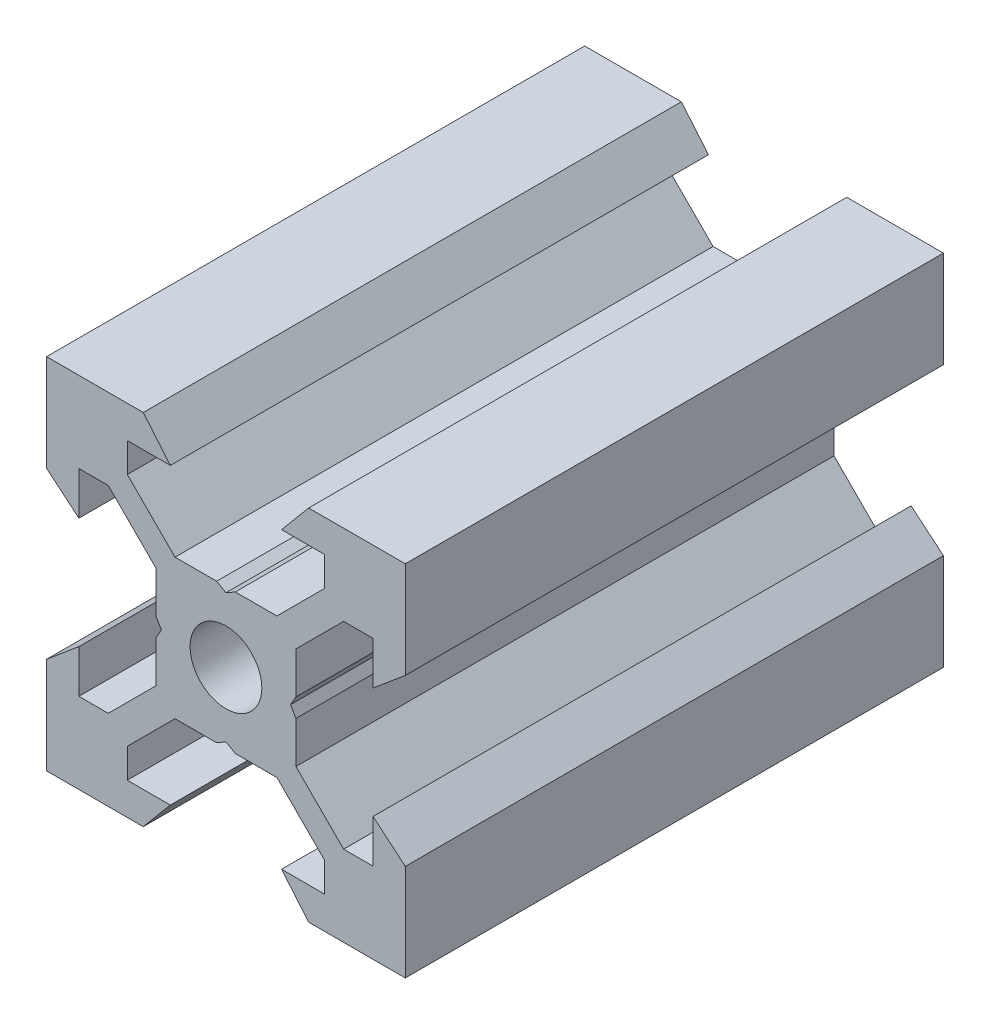
SolidWorks part; units mm, degrees
ref_plane "Front Plane" through (0, 0, 0) normal (0, 0, 1) x (1, 0, 0)
ref_plane "Top Plane" through (0, 0, 0) normal (0, 1, 0) x (1, 0, 0)
ref_plane "Right Plane" through (0, 0, 0) normal (1, 0, 0) x (0, 0, -1)
sketch "Sketch1" plane through (0, 0, 0) normal (0, 0, 1) x (1, 0, 0)
  line L0 (10, 10) -> (4.6104, 10) construction
  line L1 (10, 10) -> (10, 4.6104) construction
  line L2 (10, -10) -> (10, -4.6104) construction
  line L3 (10, -10) -> (4.6104, -10) construction
  line L4 (10, 10) -> (10, 4.6104)
  line L5 (6.5607, 5.5) -> (8.2, 5.5)
  line L6 (5.5, 8.2) -> (5.5, 6.5607)
  line L7 (10, 10) -> (4.6104, 10)
  line L8 (10, 10) -> (10, 4.6104)
  line L9 (6.5607, 5.5) -> (3.9, 2.8393)
  line L10 (5.5, 6.5607) -> (2.8393, 3.9)
  line L11 (10, 4.6104) -> (8.2, 3.1)
  line L12 (4.6104, 10) -> (3.1, 8.2)
  line L13 (8.2, 3.1) -> (8.2, 5.5)
  line L14 (3.1, 8.2) -> (5.5, 8.2)
  line L15 (-6.5607, 5.5) -> (-8.2, 5.5)
  line L16 (6.5607, -5.5) -> (8.2, -5.5)
  line L17 (3.1, -8.2) -> (5.5, -8.2)
  line L18 (8.2, -3.1) -> (8.2, -5.5)
  line L19 (4.6104, -10) -> (3.1, -8.2)
  line L20 (10, -4.6104) -> (8.2, -3.1)
  line L21 (0.5196, -3.9) -> (0, -3.6)
  line L22 (0.5196, 3.9) -> (0, 3.6)
  line L23 (3.6, 0) -> (3.9, -0.5196)
  line L24 (3.9, 0.5196) -> (3.6, 0)
  line L25 (3.9, 0.5196) -> (3.9, 2.8393)
  line L26 (2.8393, 3.9) -> (0.5196, 3.9)
  line L27 (3.9, -2.8393) -> (3.9, -0.5196)
  line L28 (2.8393, -3.9) -> (0.5196, -3.9)
  line L29 (5.5, -6.5607) -> (2.8393, -3.9)
  line L30 (6.5607, -5.5) -> (3.9, -2.8393)
  line L31 (10, -10) -> (10, -4.6104)
  line L32 (10, -10) -> (4.6104, -10)
  line L33 (5.5, -8.2) -> (5.5, -6.5607)
  line L34 (-6.5607, -5.5) -> (-8.2, -5.5)
  line L35 (10, -10) -> (10, -4.6104)
  line L36 (0, 0) -> (0, 8.2) construction
  line L37 (-10, -10) -> (-4.6104, -10) construction
  line L38 (-10, -10) -> (-10, -4.6104) construction
  line L39 (-10, 10) -> (-10, 4.6104) construction
  line L40 (-10, 10) -> (-4.6104, 10) construction
  line L41 (-10, -10) -> (-10, -4.6104)
  line L43 (-5.5, -8.2) -> (-5.5, -6.5607)
  line L44 (-10, -10) -> (-4.6104, -10)
  line L45 (-10, -10) -> (-10, -4.6104)
  line L46 (-6.5607, -5.5) -> (-3.9, -2.8393)
  line L47 (-5.5, -6.5607) -> (-2.8393, -3.9)
  line L48 (-2.8393, -3.9) -> (-0.5196, -3.9)
  line L49 (-3.9, -2.8393) -> (-3.9, -0.5196)
  line L50 (-2.8393, 3.9) -> (-0.5196, 3.9)
  line L51 (-3.9, 0.5196) -> (-3.9, 2.8393)
  line L52 (-3.9, 0.5196) -> (-3.6, 0)
  line L53 (-3.6, 0) -> (-3.9, -0.5196)
  line L54 (-0.5196, 3.9) -> (0, 3.6)
  line L55 (-0.5196, -3.9) -> (0, -3.6)
  line L56 (-10, -4.6104) -> (-8.2, -3.1)
  line L57 (-4.6104, -10) -> (-3.1, -8.2)
  line L58 (-8.2, -3.1) -> (-8.2, -5.5)
  line L59 (-3.1, -8.2) -> (-5.5, -8.2)
  line L60 (-10, -10) -> (10, -10) construction
  line L61 (-10, -10) -> (-10, 10) construction
  line L62 (-3.1, 8.2) -> (-5.5, 8.2)
  line L63 (-8.2, 3.1) -> (-8.2, 5.5)
  line L64 (-4.6104, 10) -> (-3.1, 8.2)
  line L65 (-10, 4.6104) -> (-8.2, 3.1)
  line L66 (-5.5, 6.5607) -> (-2.8393, 3.9)
  line L67 (-6.5607, 5.5) -> (-3.9, 2.8393)
  line L68 (-10, 10) -> (-10, 4.6104)
  line L69 (-10, 10) -> (-4.6104, 10)
  line L70 (-5.5, 8.2) -> (-5.5, 6.5607)
  line L71 (-10, 10) -> (10, 10) construction
  line L72 (-10, 10) -> (-10, 4.6104)
  line L73 (10, -10) -> (10, 10) construction
  line L74 (-10, -10) -> (10, 10) construction
  line L75 (-10, 10) -> (10, -10) construction
  circle A0 centre (0, 0) radius 2
  dimension "D7" = 4
  dimension "D1" = 20
  dimension "D2" = 5.3896
  dimension "D3" = 4.5
  dimension "D4" = 50
  dimension "D5" = 1.8
  dimension "D6" = 1.5104
  dimension "D8" = 5.5
  dimension "D9" = 120
  dimension "D10" = 0.3
  dimension "D11" = 2.3197
  dimension "D12" = 7.8
  dimension "D13" = 7.8
  dimension "D14" = 1.5
  dimension "D15" = 2.6607
extrude "Boss-Extrude1" add sketch "Sketch1" along normal mid plane 30 contours L70 L62 L64 L69 L68 L65 L63 L15 L67 L51 L52 L53 L49 L46 L34 L58 L56 L41 L44 L57 L59 L43 L47 L48 L55 L21 L28 L29 L33 L17 L19 L32 L31 L20 L18 L16 L30 L27 L23 L24 L25 L9 L5 L13 L11 L4 L7 L12 L14 L6 L10
